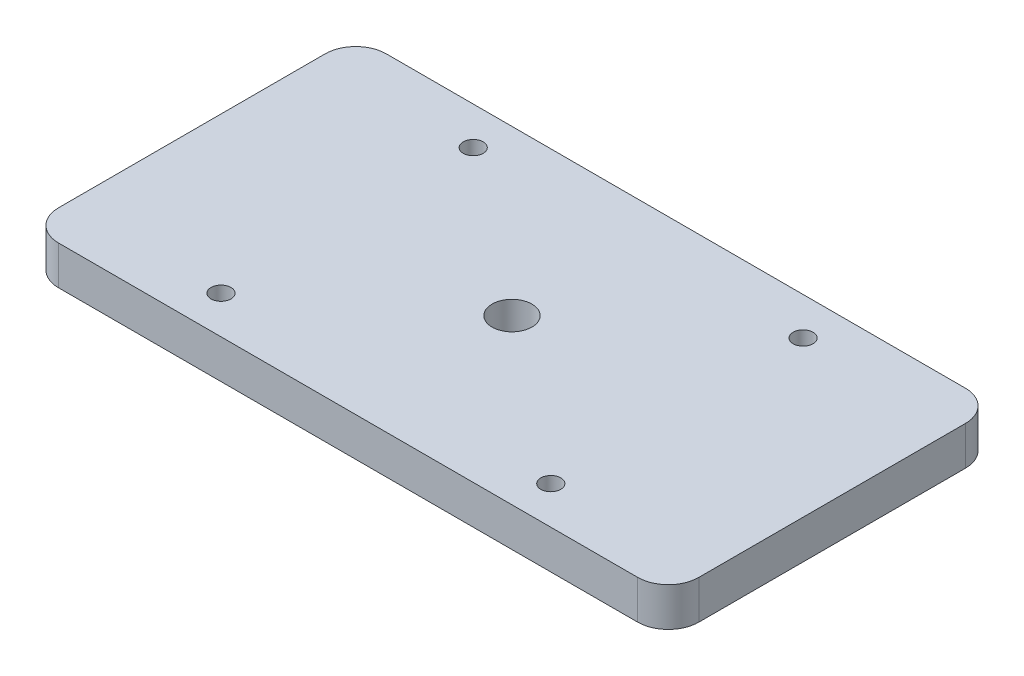
SolidWorks part; units mm, degrees
ref_plane "Front Plane" through (0, 0, 0) normal (0, 0, 1) x (1, 0, 0)
ref_plane "Top Plane" through (0, 0, 0) normal (0, 1, 0) x (1, 0, 0)
ref_plane "Right Plane" through (0, 0, 0) normal (1, 0, 0) x (0, 0, -1)
sketch "Sketch1" plane through (0, 0, 0) normal (0, 1, 0) x (1, 0, 0)
  line L1 (0, 53.63) -> (104.775, 53.63)
  line L2 (0, 53.63) -> (0, 0)
  line L3 (0, 0) -> (104.775, 0)
  line L4 (104.775, 53.63) -> (104.775, 0)
  dimension "dim1" = 104.775
  dimension "dim2" = 53.63
extrude "Boss-Extrude1" add sketch "Sketch1" along normal blind 6.35
sketch "Sketch3" plane through (0, 0, 0) normal (0, -1, 0) x (1, 0, 0)
  line L0 (104.775, 0) -> (104.775, -53.63) construction
  line L1 (0, 0) -> (104.775, 0) construction
  point P0 (52.385, -26.815)
  dimension "D1" = 52.39
  dimension "D2" = 26.815
hole_wizard "F (0.257) Diameter Hole1" positions "Sketch4" profile "Sketch5" hole size "F" standard "ANSI Inch" end condition through all
sketch "Sketch4" plane through (0, 0, 0) normal (0, -1, 0) x (-1, 0, 0)
  point P0 (-52.385, 26.815)
sketch "Sketch5" plane through (52.385, 0, -26.815) normal (1, 0, 0) x (0, 0, -1)
  line L0 (0, 0) -> (0, 6.35)
  line L1 (0, 6.35) -> (3.2639, 6.35)
  line L2 (3.2639, 6.35) -> (3.2639, 0)
  line L5 (3.2639, 0) -> (0, 0)
  line L11 (0, -6.35) -> (0, 107.95) construction
  dimension "Thru Hole Dia." = 6.5278
  dimension "Thru Hole Depth" = 6.35
fillet "Fillet1" radius 5 4 edges at (0, 3.175, -53.63) (0, 3.175, 0) (104.775, 3.175, -53.63) (104.775, 3.175, 0)
sketch "Sketch7" plane through (0, 0, 0) normal (0, -1, 0) x (1, 0, 0)
  circle A0 centre (79.375, -6.1775) radius 1.4224
  circle A1 centre (79.375, -6.1775) radius 1.4224
  circle A2 centre (25.4, -6.1775) radius 1.4224
  circle A3 centre (25.4, -6.1775) radius 1.4224
  circle A4 centre (79.375, -47.4525) radius 1.4224
  circle A5 centre (79.375, -47.4525) radius 1.4224
  circle A6 centre (25.4, -47.4525) radius 1.4224
  circle A7 centre (25.4, -47.4525) radius 1.4224
hole_wizard "#30 (0.1285) Diameter Hole1" positions "Sketch8" profile "Sketch9" hole size "#30" standard "ANSI Inch" end condition through all
sketch "Sketch8" plane through (0, 0, 0) normal (0, -1, 0) x (-1, 0, 0)
  point P0 (-25.4, 6.1775)
  point P3 (-25.4, 47.4525)
  point P6 (-79.375, 47.4525)
  point P9 (-79.375, 6.1775)
sketch "Sketch9" plane through (25.4, 0, -6.1775) normal (1, 0, 0) x (0, 0, -1)
  line L0 (0, 0) -> (0, 6.35)
  line L1 (0, 6.35) -> (1.6319, 6.35)
  line L2 (1.6319, 6.35) -> (1.6319, 0)
  line L5 (1.6319, 0) -> (0, 0)
  line L11 (0, -6.35) -> (0, 107.95) construction
  dimension "Thru Hole Dia." = 3.2639
  dimension "Thru Hole Depth" = 6.35
